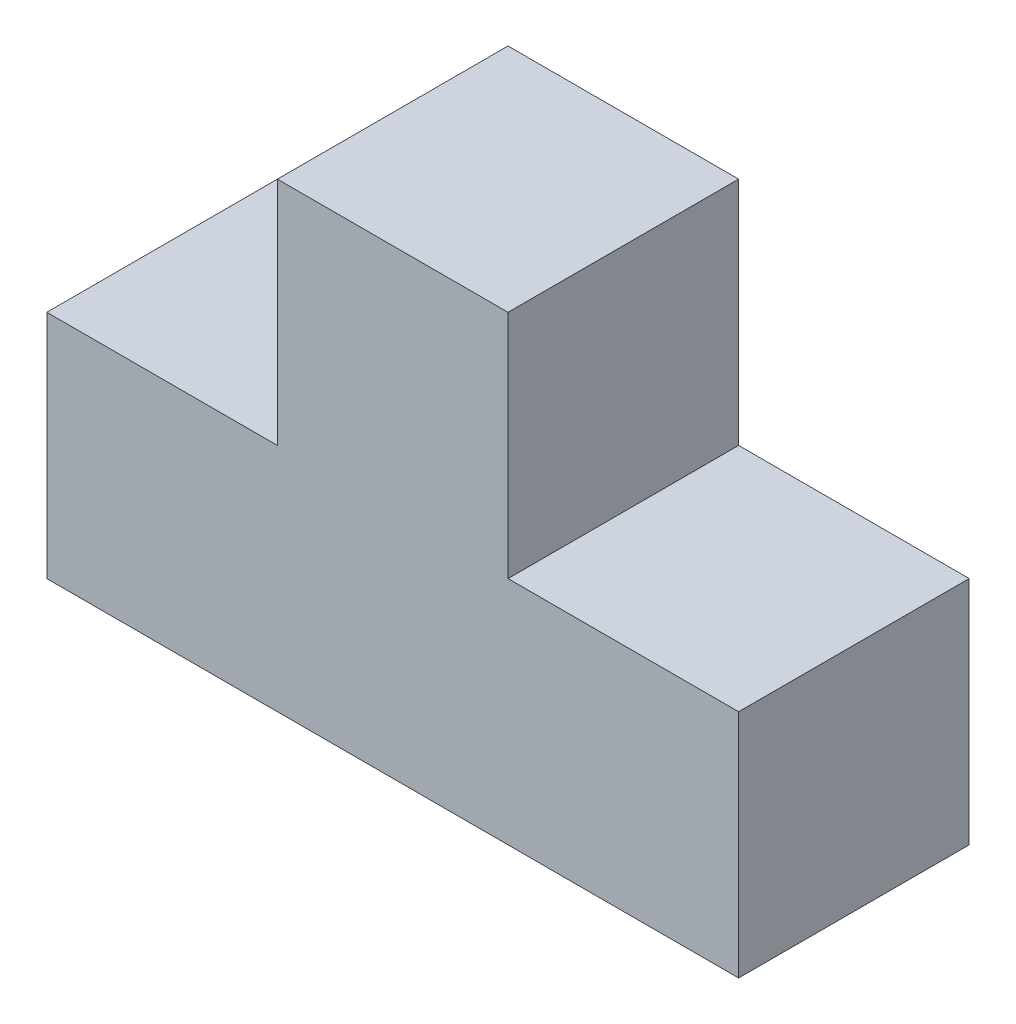
SolidWorks part; units mm, degrees
ref_plane "Plan de face" through (0, 0, 0) normal (0, 0, 1) x (1, 0, 0)
ref_plane "Plan de dessus" through (0, 0, 0) normal (0, 1, 0) x (1, 0, 0)
ref_plane "Plan de droite" through (0, 0, 0) normal (1, 0, 0) x (0, 0, -1)
sketch "Esquisse2" plane through (0, 0, 0) normal (0, 0, 1) x (1, 0, 0)
  line L0 (0, 0) -> (90, 0)
  line L1 (90, 0) -> (90, 30)
  line L2 (90, 30) -> (60, 30)
  line L3 (60, 30) -> (60, 60)
  line L4 (60, 60) -> (30, 60)
  line L5 (30, 60) -> (30, 30)
  line L6 (30, 30) -> (0, 30)
  line L7 (0, 30) -> (0, 0)
  dimension "D1" = 90
  dimension "D2" = 30
  dimension "D3" = 30
  dimension "D4" = 30
  dimension "D5" = 30
  dimension "D6" = 30
extrude "Boss.-Extru.1" add sketch "Esquisse2" along normal blind 30
